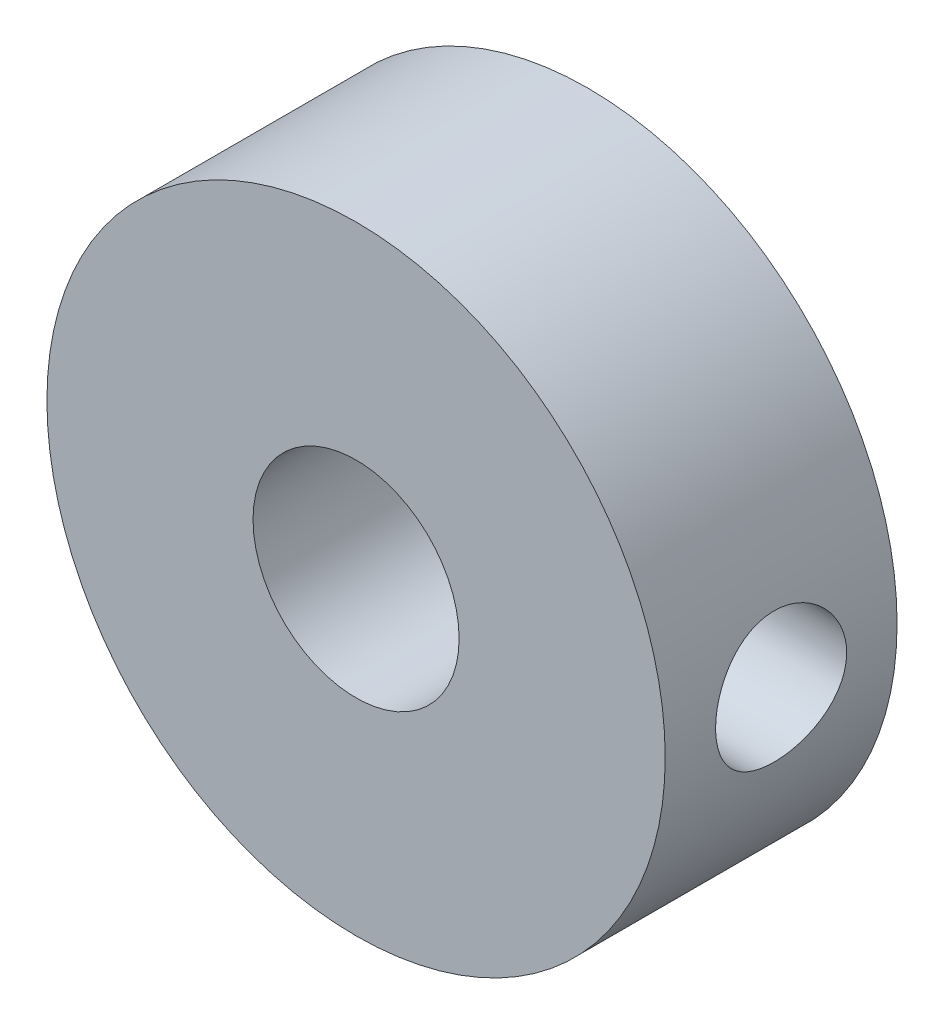
SolidWorks part; units mm, degrees
material "SS 304 (Default)"
ref_plane "Front Plane" through (0, 0, 0) normal (0, 0, 1) x (1, 0, 0)
ref_plane "Top Plane" through (0, 0, 0) normal (0, 1, 0) x (1, 0, 0)
ref_plane "Right Plane" through (0, 0, 0) normal (1, 0, 0) x (0, 0, -1)
sketch "Sketch1" plane through (0, 0, 0) normal (0, 0, 1) x (1, 0, 0)
  circle A0 centre (0, 0) radius 9.525
  circle A1 centre (0, 0) radius 3.175
  dimension "D1" = 19.05
  dimension "D2" = 6.35
extrude "Extrude1" add sketch "Sketch1" along normal mid plane 7.1437
sketch "Sketch2" plane through (0, 0, 0) normal (0, 0, 1) x (1, 0, 0)
  line L0 (0, 0) -> (9.525, 0) construction
  circle A0 centre (0, 0) radius 9.525 construction
ref_plane "Plane1" through (9.525, 0, 0) normal (1, 0, 0) x (0, 0, -1)
hole_wizard "#10-32 Tapped Hole1" positions "Sketch4" profile "Sketch3" tap size "#10-32" standard "Ansi Inch"
sketch "Sketch4" plane through (9.525, 0, 0) normal (1, 0, 0) x (0, 0, -1)
  point P0 (0, 0)
sketch "Sketch3" plane through (9.525, 0, 0) normal (0, 1, 0) x (0, 0, -1)
  line L0 (0, 0) -> (0, 6.35)
  line L1 (0, 6.35) -> (2.0193, 6.35)
  line L2 (2.0193, 6.35) -> (2.0193, 0)
  line L5 (2.0193, 0) -> (0, 0)
  line L11 (0, -6.35) -> (0, 107.95) construction
  dimension "Thru Tap Drill Dia." = 4.0386
  dimension "Thru Tap Drill Depth" = 6.35
cosmetic thread "Hole Thread1" parameters "D2"=4.826
